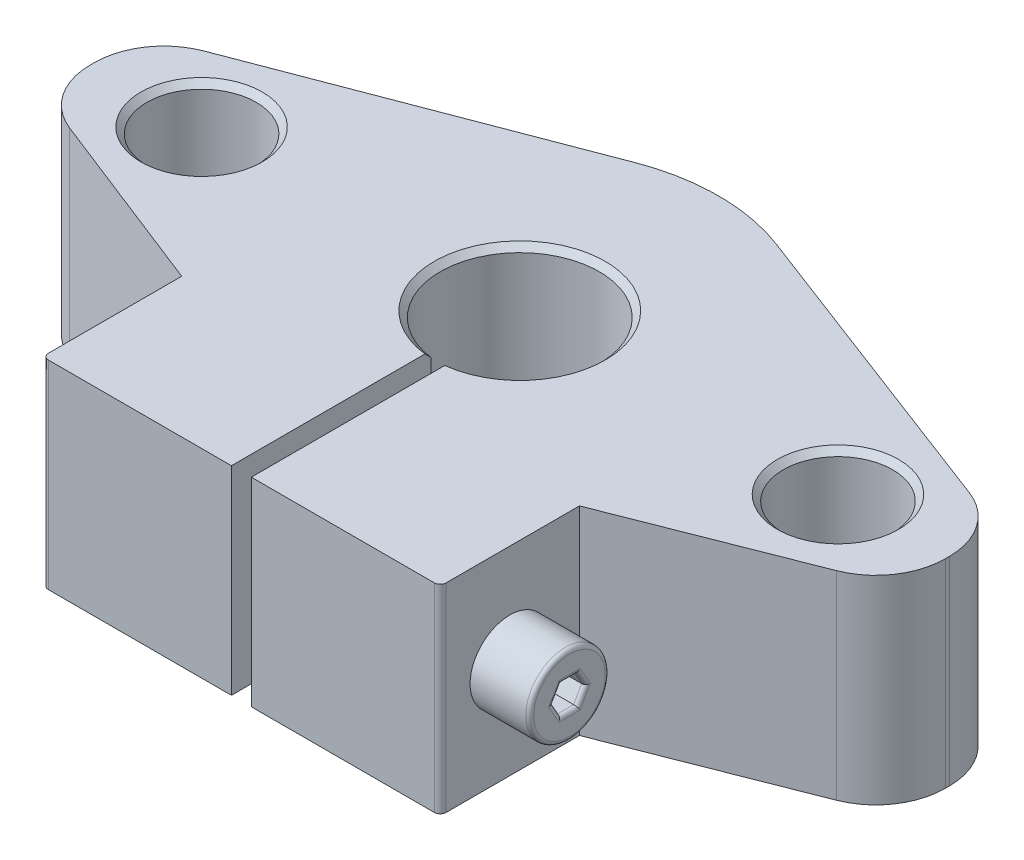
SolidWorks part; units mm, degrees
other "Kamera1"
material "АМг 2 ГОСТ 4784-97"
ref_plane "Front Plane" through (0, 0, 0) normal (0, 0, 1) x (1, 0, 0)
ref_plane "Top Plane" through (0, 0, 0) normal (0, 1, 0) x (1, 0, 0)
ref_plane "Right Plane" through (0, 0, 0) normal (1, 0, 0) x (0, 0, -1)
sketch "Sketch1" plane through (0, 0, 0) normal (0, 1, 0) x (1, 0, 0)
  line L0 (21.5, 0.1007) -> (21.5, -0.1007)
  line L1 (-21.5, 0.1007) -> (-21.5, -0.1007)
  line L2 (0, 10) -> (0, -14) construction
  line L3 (-21.5, 0) -> (21.5, 0) construction
  line L10 (16, -13.3465) -> (16, 13.603) construction
  line L13 (-16, -13.3465) -> (-16, 13.603) construction
  line L15 (0.5, -3.9686) -> (0.5, -14)
  line L20 (0.5, -14) -> (10, -14)
  line L24 (10, -14) -> (10, -7)
  line L25 (-10, -14) -> (-10, -7)
  line L26 (-0.5, -14) -> (-10, -14)
  line L27 (-0.5, -3.9686) -> (-0.5, -14)
  line L28 (19.2786, -3.3588) -> (10, -7)
  line L29 (19.2456, 3.3715) -> (3.5588, 9.3453)
  line L30 (-19.2456, 3.3715) -> (-3.5588, 9.3453)
  line L31 (-19.2786, -3.3588) -> (-10, -7)
  arc A0 (21.5, -0.1007) -> (19.2786, -3.3588) centre (18, -0.1007) cw
  arc A1 (21.5, 0.1007) -> (19.2456, 3.3715) centre (18, 0.1007) ccw
  circle A2 centre (-16, 0) radius 2.75
  circle A3 centre (16, 0) radius 2.75
  arc A4 (-21.5, -0.1007) -> (-19.2786, -3.3588) centre (-18, -0.1007) ccw
  arc A5 (-21.5, 0.1007) -> (-19.2456, 3.3715) centre (-18, 0.1007) cw
  arc A12 (-3.5588, 9.3453) -> (3.5588, 9.3453) centre (0, 0) cw
  arc A13 (-0.5, -3.9686) -> (0.5, -3.9686) centre (0, 0) cw
  point P5 (-21.5, 13.3465)
  point P6 (-21.5, -13.603)
  point P7 (21.5, 13.3465)
  point P8 (21.5, -13.603)
  point P20 (0, 10)
  point P22 (21.5, -2.487)
  point P26 (21.5, 2.513)
  dimension "D1" = 43
  dimension "D4" = 1
  dimension "D7" = 5.5
  dimension "D8" = 16
  dimension "D6" = 24
  dimension "D2" = 4
  dimension "D5" = 7
  dimension "D11" = 3.5
  dimension "D9" = 5
  dimension "D10" = 10
  dimension "D3" = 20
extrude "Boss-Extrude1" add sketch "Sketch1" along normal blind 10
sketch "Sketch3" plane through (10, 0, 0) normal (1, 0, 0) x (0, 0, -1)
  line L1 (-7, 5) -> (-14, 5) construction
  line L2 (-7, 10) -> (-7, 0) construction
  line L3 (-14, 10) -> (-14, 0) construction
  line L4 (-10.5, 10) -> (-10.5, 0) construction
  line L5 (-14, 10) -> (-7, 10) construction
  line L6 (-14, 0) -> (-7, 0) construction
  circle A0 centre (-10.5, 5) radius 2
  point P15 (-10.5, 5)
  dimension "D1" = 4
extrude "Cut-Extrude1" cut sketch "Sketch3" against normal through all
sketch "Esboço1" plane through (10, 0, 0) normal (-1, 0, 0) x (0, 0, 1)
  circle A0 centre (10.5, 5) radius 2 construction
  circle A1 centre (10.5, 5) radius 2
  dimension "D1" = 4
extrude "Ressalto-extrusão2" add sketch "Esboço1" along normal blind 13 and the other way blind 3
sketch "Esboço2" plane through (13, 0, 0) normal (-1, 0, 0) x (0, 0, 1)
  line L0 (8.5, 5) -> (12.5, 5) construction
  line L2 (11.3155, 5) -> (10.9078, 5.7063)
  line L3 (10.9078, 5.7063) -> (10.0922, 5.7063)
  line L4 (10.0922, 5.7063) -> (9.6845, 5)
  line L5 (9.6845, 5) -> (10.0922, 4.2937)
  line L6 (10.0922, 4.2937) -> (10.9078, 4.2937)
  line L7 (10.9078, 4.2937) -> (11.3155, 5)
  circle A0 centre (10.5, 5) radius 2 construction
  circle A2 centre (10.5, 5) radius 0.7063 construction
  point P5 (10.5, 5)
extrude "Corte-extrusão1" cut sketch "Esboço2" along normal blind 5 from surface at 0 contours L7 L6 L5 L4 L3 L2 starting at face at (13, 5, 12.5)
fillet "Filete1" radius 0.2 7 edges at (13, 5, 12.5) (13, 5.3531, 11.1117) (13, 5.7063, 10.5) (13, 5.3531, 9.8883) (13, 4.6469, 9.8883) (13, 4.2937, 10.5) (13, 4.6469, 11.1117)
fillet "Filete2" radius 0.25 1 edges at (-3, 5, 12.5)
chamfer "Фаска1" distance 0.3 angle 45 6 edges at (-16, 0, 2.75) (0, 0, -4) (16, 0, 2.75) (16, 10, 2.75) (-16, 10, 2.75) (0, 10, -4)
fillet "Скругление1" radius 0.3 2 edges at (-10, 5, 14) (10, 5, 14)
